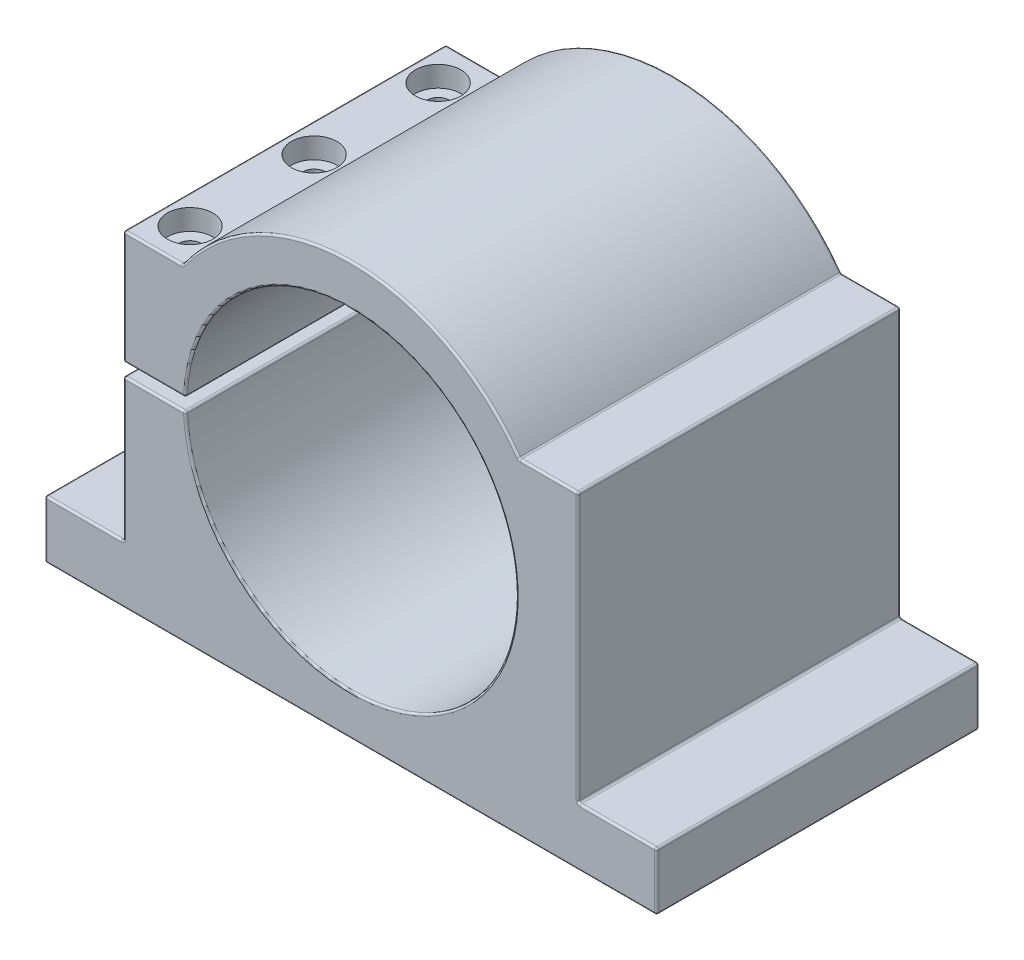
SolidWorks part; units mm, degrees
ref_plane "Спереди" through (0, 0, 0) normal (0, 0, 1) x (1, 0, 0)
ref_plane "Сверху" through (0, 0, 0) normal (0, 1, 0) x (1, 0, 0)
ref_plane "Справа" through (0, 0, 0) normal (1, 0, 0) x (0, 0, -1)
sketch "Эскиз1" plane through (0, 0, 0) normal (0, 0, 1) x (1, 0, 0)
  line L0 (0, 0) -> (0, -50) construction
  line L1 (74, -50) -> (-74, -50)
  line L2 (-74, -50) -> (-74, -36)
  line L3 (-74, -36) -> (-55, -36)
  line L4 (-55, -36) -> (-55, 29)
  line L5 (-55, 29) -> (-40.7308, 29)
  line L6 (0, 29) -> (-40.7308, 29) construction
  line L7 (-55, 1.5) -> (0, 1.5)
  line L8 (-55, 1.5) -> (-55, -1.5)
  line L9 (-55, -1.5) -> (0, -1.5)
  line L10 (0, 1.5) -> (0, -1.5)
  line L11 (0, 29) -> (0, 0) construction
  line L12 (0, -50) -> (0, 50) construction
  line L13 (55, 29) -> (40.7308, 29)
  line L14 (55, -36) -> (55, 29)
  line L15 (74, -36) -> (55, -36)
  line L16 (74, -50) -> (74, -36)
  circle A0 centre (0, 0) radius 40
  circle A2 centre (0, 0) radius 50
  point P13 (-27.55, 29)
  point P20 (0, 40)
  dimension "D1" = 80
  dimension "D2" = 3
  dimension "D3" = 50
  dimension "D4" = 14
  dimension "D5" = 148
  dimension "D6" = 19
  dimension "D7" = 65
  dimension "D8" = 10
extrude "Бобышка-Вытянуть1" add sketch "Эскиз1" along normal mid plane 78 contours A2 L1 L16 L15 L14 L13 | A2 L7 A0 L9 | A2 L9 L4 L3 L2 L1 | A2 L5 L4 L7
sketch "Эскиз2" plane through (0, 29, 0) normal (0, 1, 0) x (1, 0, 0)
  line L0 (-47.8654, 39) -> (-47.8654, -39) construction
  line L1 (-55, 39) -> (-40.7308, 39) construction
  line L2 (-55, -39) -> (-40.7308, -39) construction
  circle A0 centre (-47.8654, 30) radius 5.5
  circle A1 centre (-47.8654, 0) radius 5.5
  circle A2 centre (-47.8654, -30) radius 5.5
  dimension "D1" = 11
  dimension "D2" = 11
  dimension "D3" = 11
  dimension "D4" = 30
  dimension "D5" = 30
extrude "Вырез-Вытянуть1" cut sketch "Эскиз2" against normal blind 5
sketch "Эскиз3" plane through (0, 24, 0) normal (0, 1, 0) x (1, 0, 0)
  circle A0 centre (-47.8654, 30) radius 2.75
  circle A1 centre (-47.8654, 0) radius 2.75
  circle A2 centre (-47.8654, -30) radius 2.75
  dimension "D1" = 5.5
extrude "Вырез-Вытянуть2" cut sketch "Эскиз3" against normal up to surface (25.5 mm away) up to face at (-47.4859, -1.5, 0)
sketch "Эскиз4" plane through (0, -1.5, 0) normal (0, 1, 0) x (1, 0, 0)
  circle A0 centre (-47.8654, 30) radius 2.1
  circle A1 centre (-47.8654, 0) radius 2.1
  circle A2 centre (-47.8654, -30) radius 2.1
  dimension "D1" = 4.2
extrude "Вырез-Вытянуть3" cut sketch "Эскиз4" against normal blind 30
fillet "Скругление1" radius 0.5 42 edges at (-74, -36, 0) (74, -36, 0) (55, -36, 0) (55, 29, 0) (-55, 29, 0) (-55, 1.5, 0) (-55, -1.5, 0) (-55, -36, 0) (40.7308, 29, 0) (-40.7308, 29, 0) (-74, -50, 0) (74, -50, 0) (0, 50, -39) (-47.8654, 29, -39) (-55, 15.25, -39) (-47.4859, 1.5, -39) (-47.4859, -1.5, -39) (-55, -18.75, -39) (-64.5, -36, -39) (-74, -43, -39) (0, -50, -39) (74, -43, -39) (64.5, -36, -39) (55, -3.5, -39) (47.8654, 29, -39) (-39.9719, 1.5, 0) (-39.9719, -1.5, 0) (40, 0, -39) (55, -3.5, 39) (64.5, -36, 39) (74, -43, 39) (0, -50, 39) (-74, -43, 39) (-64.5, -36, 39) (-55, -18.75, 39) (-47.4859, -1.5, 39) (40, 0, 39) (-47.4859, 1.5, 39) (-55, 15.25, 39) (-47.8654, 29, 39) (0, 50, 39) (47.8654, 29, 39)
